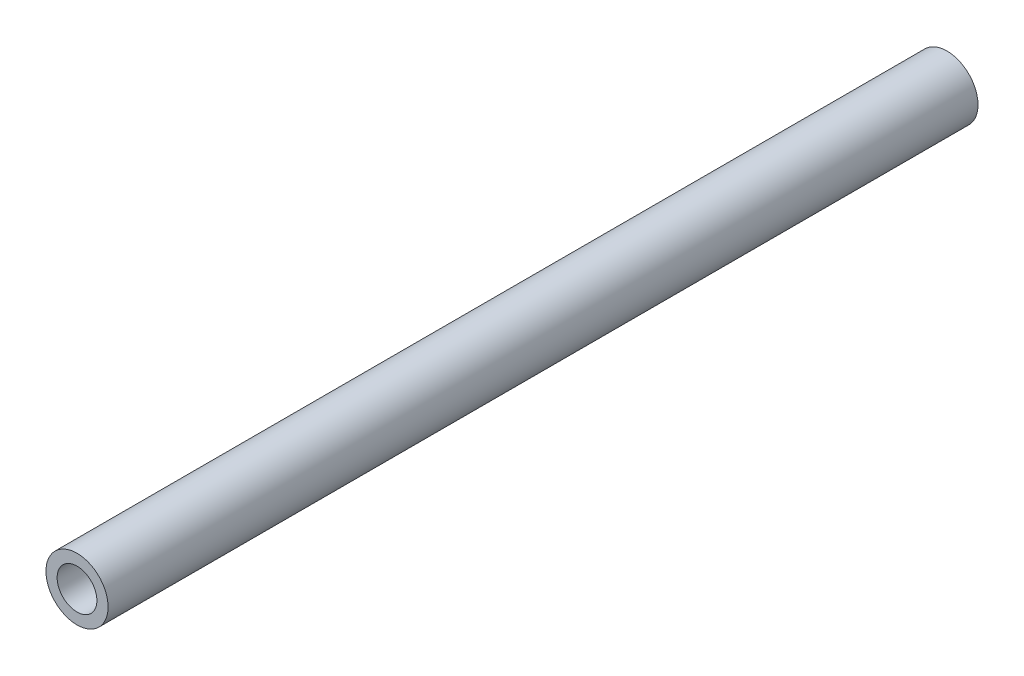
SolidWorks part; units mm, degrees
ref_plane "Front" through (0, 0, 0) normal (0, 0, 1) x (1, 0, 0)
ref_plane "Top" through (0, 0, 0) normal (0, 1, 0) x (1, 0, 0)
ref_plane "Right" through (0, 0, 0) normal (1, 0, 0) x (0, 0, -1)
sketch "Sketch1" plane through (0, 0, 0) normal (0, 0, 1) x (1, 0, 0)
  circle A0 centre (0, 0) radius 1.6
  circle A1 centre (0, 0) radius 2.5
extrude "Boss-Extrude1" add sketch "Sketch1" along normal blind 70
